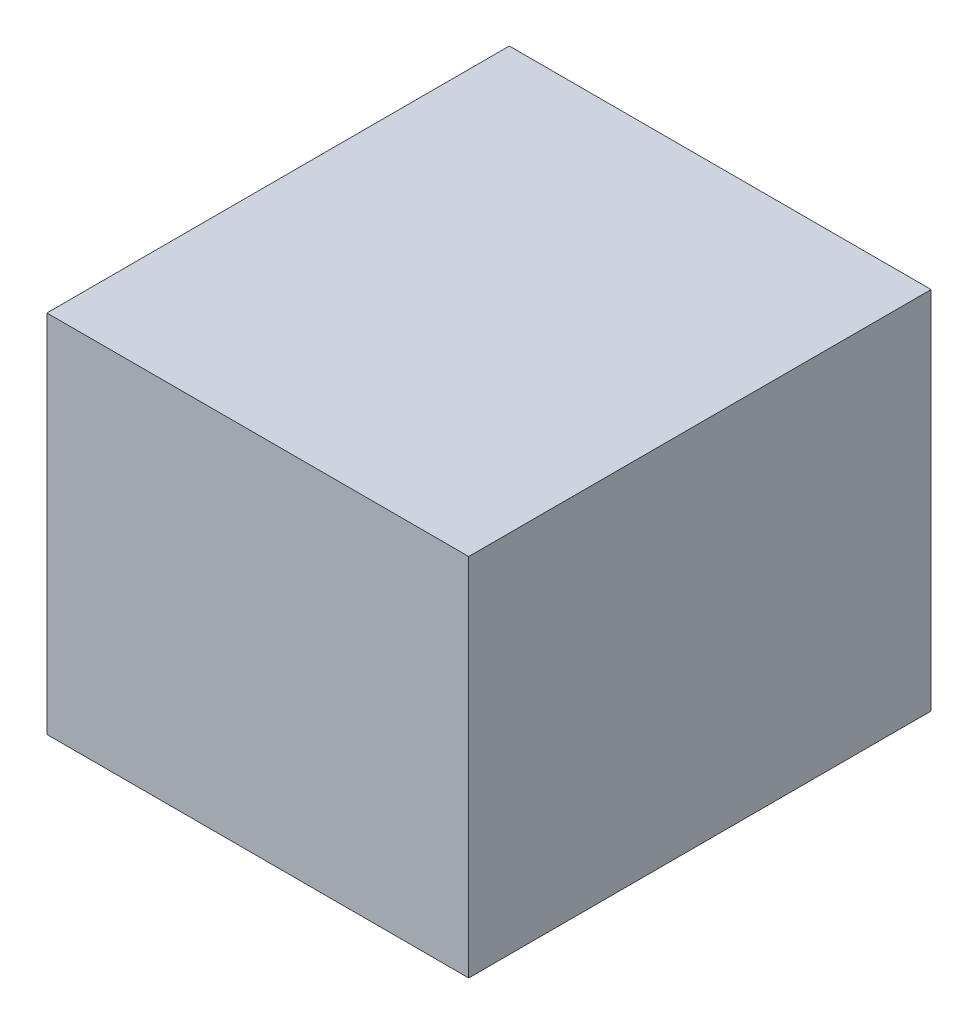
SolidWorks part; units mm, degrees
ref_plane "Front Plane" through (0, 0, 0) normal (0, 0, 1) x (1, 0, 0)
ref_plane "Top Plane" through (0, 0, 0) normal (0, 1, 0) x (1, 0, 0)
ref_plane "Right Plane" through (0, 0, 0) normal (1, 0, 0) x (0, 0, -1)
sketch "Sketch1" plane through (0, 0, 0) normal (0, 0, 1) x (1, 0, 0)
  line L1 (-260, -225) -> (260, -225)
  line L2 (-260, -225) -> (-260, 225)
  line L3 (-260, 225) -> (260, 225)
  line L4 (260, -225) -> (260, 225)
  line L5 (-260, -225) -> (260, 225) construction
  line L6 (-260, 225) -> (260, -225) construction
  point P0 (0, 0)
  dimension "D1" = 520
  dimension "D2" = 450
extrude "Boss-Extrude1" add sketch "Sketch1" along normal blind 5
sketch "Sketch3" plane through (0, 0, 0) normal (0, 0, -1) x (-1, 0, 0)
  line L0 (260, 225) -> (-260, 225)
  line L1 (260, 225) -> (260, -225)
  line L2 (-260, 225) -> (-260, -225)
  line L3 (260, -225) -> (-260, -225)
  line L4 (-260, 225) -> (260, 225) construction
  line L5 (255, -225) -> (255, 220)
  line L6 (255, -225) -> (-255, -225)
  line L7 (255, 220) -> (-255, 220)
  line L8 (-255, -225) -> (-255, 220)
  line L10 (-260, -225) -> (-155, -225)
  line L11 (-260, -225) -> (-260, -220)
  line L12 (-260, -220) -> (-155, -220)
  line L13 (-155, -225) -> (-155, -220)
  line L14 (260, -225) -> (155, -225)
  line L15 (260, -225) -> (260, -220)
  line L16 (260, -220) -> (155, -220)
  line L17 (155, -225) -> (155, -220)
  point P7 (0, 220)
  line M9 (-260, 225) -> (-260, -225)
  line M10 (-260, -225) -> (260, -225)
  line M11 (260, -225) -> (260, 225)
  line M12 (260, 225) -> (-260, 225)
  dimension "D1" = 5
  dimension "D2" = 510
  dimension "D3" = 5
  dimension "450" = 520
  dimension "D4" = 105
  dimension "D5" = 5
  dimension "D6" = 105
extrude "Boss-Extrude3" add sketch "Sketch3" along normal blind 560 contours L3 L8 L7 L5 M11 M12 M9 | L17 L3 L5 L16 | L12 L2 L8 M10 | L16 L5 L3 M11
sketch "Sketch4" plane through (0, 0, -560) normal (0, 0, -1) x (-1, 0, 0)
  line L0 (260, 225) -> (-260, 225)
  line L1 (260, 225) -> (260, -225)
  line L2 (-260, 225) -> (-260, -225)
  line L3 (260, -225) -> (-260, -225)
  dimension "D1" = 450
extrude "Boss-Extrude4" add sketch "Sketch4" along normal blind 5
sketch "Sketch5" plane through (0, 0, -560) normal (0, 0, 1) x (1, 0, 0)
  line L0 (-260, -225) -> (260, -225)
  line L1 (-260, -225) -> (-260, 225)
  line L2 (260, -225) -> (260, 225)
  line L3 (-260, 225) -> (260, 225)
  line L4 (155, -225) -> (-155, -225) construction
  line L13 (-255, 220) -> (255, 220)
  line L14 (-255, 220) -> (-255, -220)
  line L15 (-255, -220) -> (255, -220)
  line L16 (255, 220) -> (255, -220)
  line L17 (-255, 220) -> (255, -220) construction
  line L18 (-255, -220) -> (255, 220) construction
  point P9 (0, -329.1162)
  point P14 (0, 0)
  dimension "D1" = 450
  dimension "D2" = 510
  dimension "D3" = 440
extrude "Boss-Extrude5" add sketch "Sketch5" along normal blind 100
sketch "Sketch6" plane through (0, -225, 0) normal (0, -1, 0) x (1, 0, 0)
  line L0 (-169.55, 5) -> (-169.55, -565) construction
  line L1 (-260, 5) -> (260, 5) construction
  line L2 (260, -565) -> (-260, -565) construction
  line L3 (-155, -460) -> (-155, 0) construction
  line L4 (-155, -460) -> (155, -460) construction
  line L5 (-155, 0) -> (155, 0) construction
  circle A0 centre (-169.55, -10) radius 2.5
  circle A1 centre (-169.55, -36) radius 2.5
  circle A2 centre (-169.55, -450) radius 2.5
  circle A3 centre (-169.55, -424) radius 2.5
  dimension "D3" = 5
  dimension "D4" = 26
  dimension "D1" = 14.55
  dimension "D2" = 26
  dimension "D5" = 10
  dimension "D6" = 10
extrude "Cut-Extrude1" cut sketch "Sketch6" against normal blind 10
